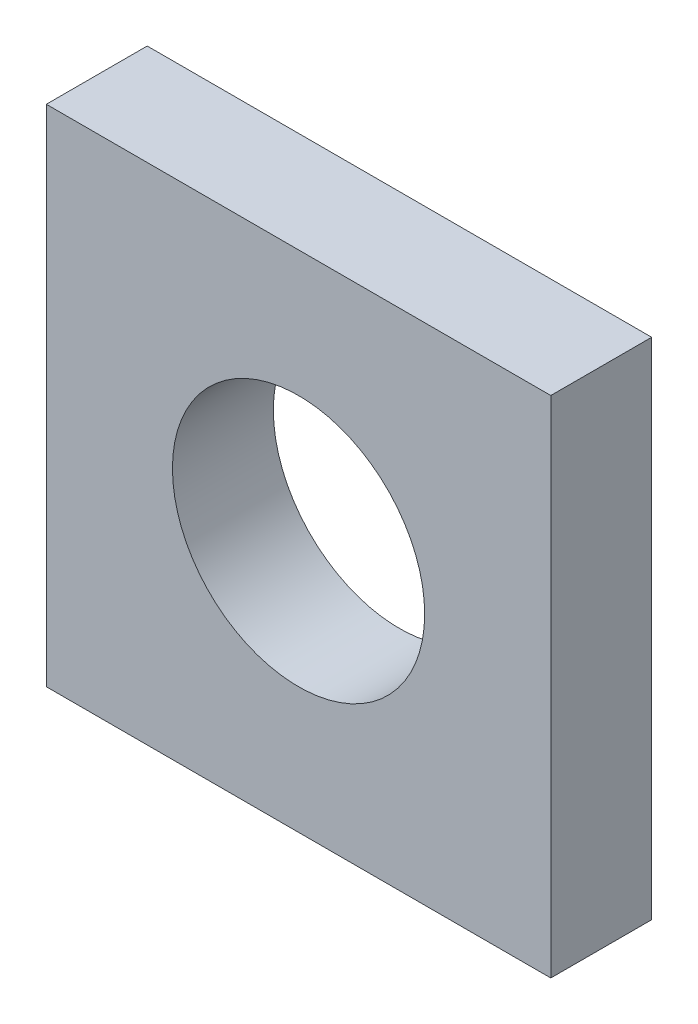
SolidWorks part; units mm, degrees
ref_plane "Plan de face" through (0, 0, 0) normal (0, 0, 1) x (1, 0, 0)
ref_plane "Plan de dessus" through (0, 0, 0) normal (0, 1, 0) x (1, 0, 0)
ref_plane "Plan de droite" through (0, 0, 0) normal (1, 0, 0) x (0, 0, -1)
sketch "Esquisse4" plane through (0, 0, 0) normal (0, 0, 1) x (1, 0, 0)
  line L1 (-77.5684, -19.4876) -> (-27.5684, -19.4876)
  line L2 (-77.5684, -19.4876) -> (-77.5684, -69.4876)
  line L3 (-77.5684, -69.4876) -> (-27.5684, -69.4876)
  line L4 (-27.5684, -19.4876) -> (-27.5684, -69.4876)
  line L5 (-77.5684, -19.4876) -> (-27.5684, -69.4876) construction
  line L6 (-77.5684, -69.4876) -> (-27.5684, -19.4876) construction
  circle A0 centre (-52.5684, -44.4876) radius 12.5
  point P0 (-52.5684, -44.4876)
extrude "Boss.-Extru.4" add sketch "Esquisse4" along normal mid plane 10
